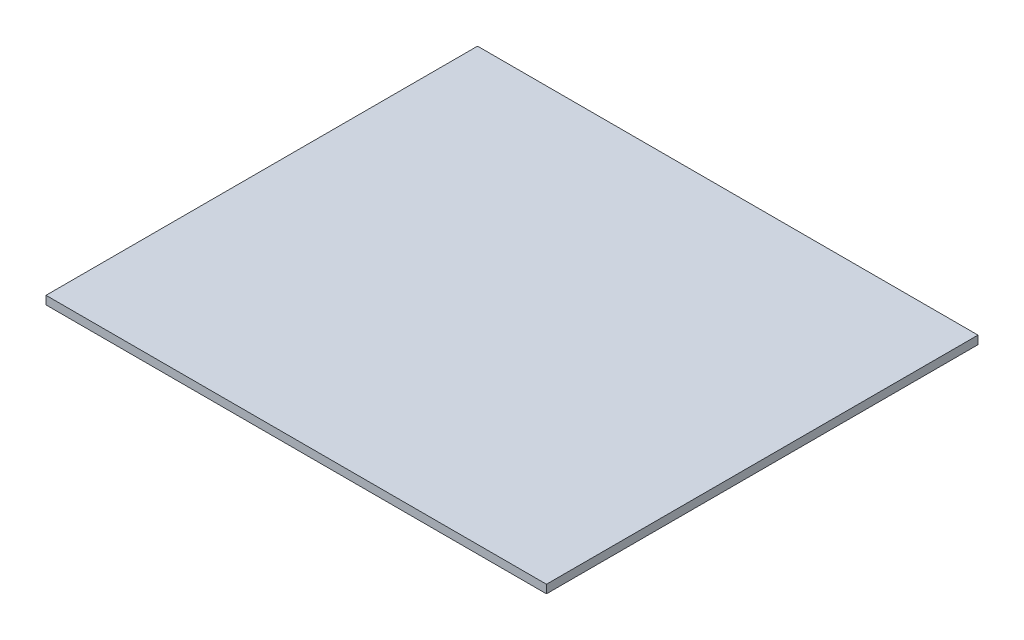
SolidWorks part; units mm, degrees
ref_plane "Front Plane" through (0, 0, 0) normal (0, 0, 1) x (1, 0, 0)
ref_plane "Top Plane" through (0, 0, 0) normal (0, 1, 0) x (1, 0, 0)
ref_plane "Right Plane" through (0, 0, 0) normal (1, 0, 0) x (0, 0, -1)
sketch "Sketch1" plane through (0, 0, 0) normal (0, 1, 0) x (1, 0, 0)
  line L0 (-100, 0) -> (500, 0)
  line L1 (-100, 0) -> (-100, 517.37)
  line L2 (-100, 0) -> (-100, 7)
  line L3 (-100, 7) -> (500, 7)
  line L4 (500, 7) -> (500, 0)
  line L5 (500, 0) -> (500, 517.37)
  line L6 (500, 517.37) -> (-100, 517.37)
  line L7 (500, 517.37) -> (500, 510.37)
  line L8 (500, 510.37) -> (-100, 510.37)
extrude "Boss-Extrude1" add sketch "Sketch1" along normal blind 10 contours L5 L8 L1 L3 | L8 L5 L6 L1 | L4 L3 L1 L0
